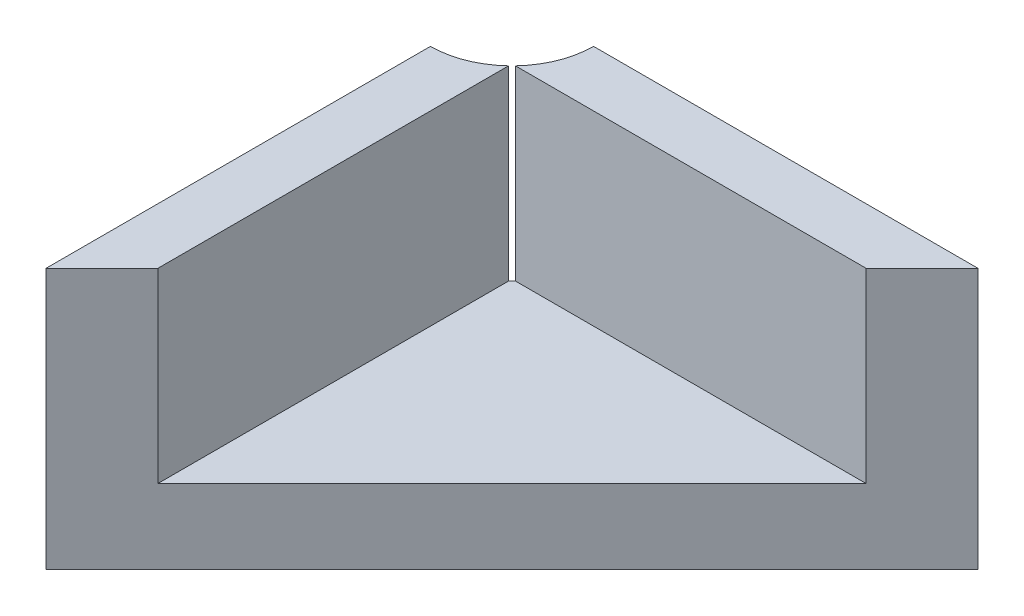
SolidWorks part; units mm, degrees
ref_plane "Front Plane" through (0, 0, 0) normal (0, 0, 1) x (1, 0, 0)
ref_plane "Top Plane" through (0, 0, 0) normal (0, 1, 0) x (1, 0, 0)
ref_plane "Right Plane" through (0, 0, 0) normal (1, 0, 0) x (0, 0, -1)
sketch "Sketch2" plane through (0, 0, 0) normal (0, 1, 0) x (1, 0, 0)
  line L1 (5, 5) -> (-5, 5)
  line L2 (5, 5) -> (5, -5)
  line L3 (5, -5) -> (-5, -5)
  line L4 (-5, 5) -> (-5, -5)
  line L5 (5, 5) -> (-5, -5) construction
  line L6 (5, -5) -> (-5, 5) construction
  point P0 (0, 0)
  dimension "D1" = 10
  dimension "D2" = 10
extrude "Boss-Extrude1" add sketch "Sketch2" along normal blind 1.6
sketch "Sketch4" plane through (0, 1.6, 0) normal (0, 1, 0) x (1, 0, 0)
  line L1 (5, 5) -> (-5, 5)
  line L2 (5, 5) -> (5, -5)
  line L3 (5, -5) -> (-5, -5)
  line L4 (-5, 5) -> (-5, -5)
  line L5 (5, 5) -> (-5, -5) construction
  line L6 (5, -5) -> (-5, 5) construction
  point P0 (0, 0)
extrude "Extrude-Thin1" add sketch "Sketch4" along normal blind 4 thin thin type one direction reverse wall 1.2
sketch "Sketch5" plane through (0, 0, 0) normal (0, -1, 0) x (1, 0, 0)
  line L0 (-5, 5) -> (5, 5)
  line L1 (5, 5) -> (5, -5)
  line L2 (5, -5) -> (-5, 5)
extrude "Cut-Extrude1" cut sketch "Sketch5" against normal blind 5.6
sketch "Sketch6" plane through (0, 0, 0) normal (0, -1, 0) x (1, 0, 0)
  circle A0 centre (-5, -5) radius 1.75
extrude "Cut-Extrude2" cut sketch "Sketch6" against normal blind 5.6
